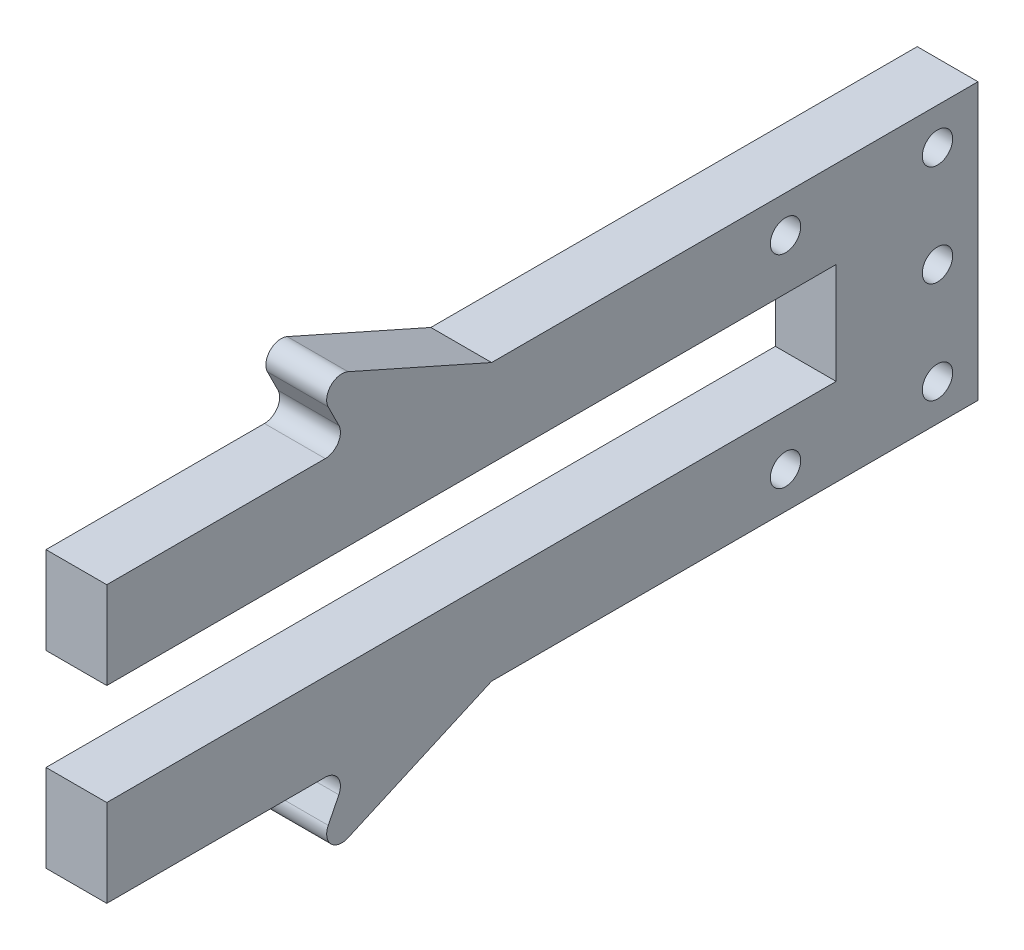
SolidWorks part; units mm, degrees
material "Custom Plastic"
ref_plane "Front Plane" through (0, 0, 0) normal (0, 0, 1) x (1, 0, 0)
ref_plane "Top Plane" through (0, 0, 0) normal (0, 1, 0) x (1, 0, 0)
ref_plane "Right Plane" through (0, 0, 0) normal (1, 0, 0) x (0, 0, -1)
sketch "Sketch2" plane through (0, 0, 0) normal (1, 0, 0) x (0, 0, -1)
  line L0 (-20.9136, -4.3885) -> (-8.9196, -4.3885)
  line L1 (22.0864, -4.3885) -> (22.0864, -18.0092)
  line L2 (22.0864, -18.0092) -> (-1.9196, -18.0092)
  line L3 (-20.9136, -18.0092) -> (-20.9136, -13.6989)
  line L4 (-20.9136, -13.6989) -> (15.0864, -13.6989)
  line L5 (15.0864, -13.6989) -> (15.0864, -8.6989)
  line L6 (15.0864, -8.6989) -> (-20.9136, -8.6989)
  line L7 (-20.9136, -8.6989) -> (-20.9136, -4.3885)
  line L8 (-1.9196, -4.3885) -> (-10.9136, -0.3885)
  line L9 (-10.9136, -0.3885) -> (-8.9196, -4.3885)
  line L10 (22.0864, -11.1989) -> (-19.6352, -11.1989) construction
  line L11 (-10.9136, -22.0092) -> (-8.9196, -18.0092)
  line L12 (-1.9196, -18.0092) -> (-10.9136, -22.0092)
  line L13 (-1.9196, -4.3885) -> (22.0864, -4.3885)
  line L14 (-8.9196, -18.0092) -> (-20.9136, -18.0092)
  dimension "D1" = 5
  dimension "D2" = 36
  dimension "D3" = 43
  dimension "D4" = 4
  dimension "D5" = 7
  dimension "D6" = 10
extrude "Boss-Extrude1" add sketch "Sketch2" along normal blind 3
fillet "Fillet1" radius 0.75 4 edges at (1.5, -22.0092, 10.9136) (1.5, -18.0092, 8.9196) (1.5, -4.3885, 8.9196) (1.5, -0.3885, 10.9136)
sketch "Sketch3" plane through (3, 0, 0) normal (1, 0, 0) x (0, 0, -1)
  line L0 (20.0864, -6.1989) -> (20.0864, -16.1989) construction
  line L1 (15.0864, -8.6989) -> (15.0864, -13.6989) construction
  line L2 (15.0864, -11.1989) -> (20.0864, -11.1989) construction
  line L3 (20.0864, -6.1989) -> (12.5864, -6.1989) construction
  line L4 (20.0864, -16.1989) -> (12.5864, -16.1989) construction
  circle A0 centre (20.0864, -6.1989) radius 0.75
  circle A1 centre (20.0864, -16.1989) radius 0.75
  circle A2 centre (20.0864, -11.1989) radius 0.75
  circle A3 centre (12.5864, -6.1989) radius 0.75
  circle A4 centre (12.5864, -16.1989) radius 0.75
  dimension "D3" = 1.5
  dimension "D1" = 5
  dimension "D2" = 10
  dimension "D4" = 7.5
  dimension "D5" = 7.5
extrude "Cut-Extrude1" cut sketch "Sketch3" against normal through all
